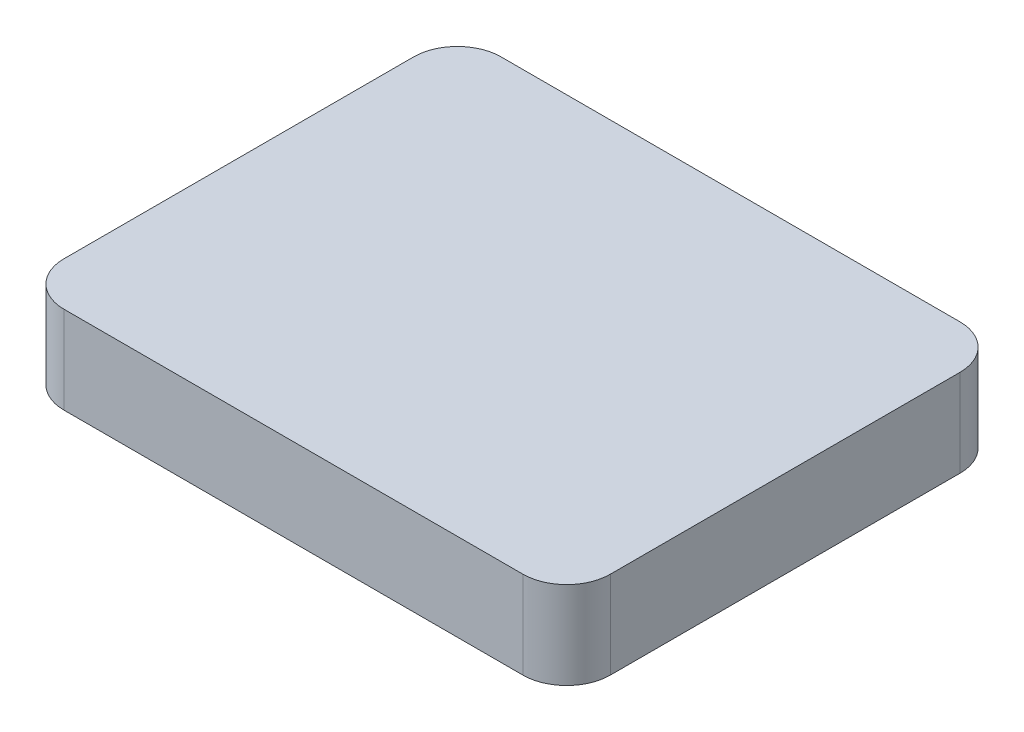
SolidWorks part; units mm, degrees
ref_plane "Front Plane" through (0, 0, 0) normal (0, 0, 1) x (1, 0, 0)
ref_plane "Top Plane" through (0, 0, 0) normal (0, 1, 0) x (1, 0, 0)
ref_plane "Right Plane" through (0, 0, 0) normal (1, 0, 0) x (0, 0, -1)
sketch "Sketch2" plane through (0, 0, 0) normal (0, 1, 0) x (1, 0, 0)
  line L1 (-105, 100) -> (105, 100)
  line L2 (-125, 80) -> (-125, -80)
  line L3 (-105, -100) -> (105, -100)
  line L4 (125, 80) -> (125, -80)
  line L5 (-125, 100) -> (125, -100) construction
  line L6 (-125, -100) -> (125, 100) construction
  arc A0 (-105, -100) -> (-125, -80) centre (-105, -80) cw
  arc A1 (105, -100) -> (125, -80) centre (105, -80) ccw
  arc A2 (125, 80) -> (105, 100) centre (105, 80) ccw
  arc A3 (-125, 80) -> (-105, 100) centre (-105, 80) cw
  point P0 (0, 0)
  dimension "D3" = 20
  dimension "D1" = 250
  dimension "D2" = 200
extrude "Boss-Extrude2" add sketch "Sketch2" along normal mid plane 40
